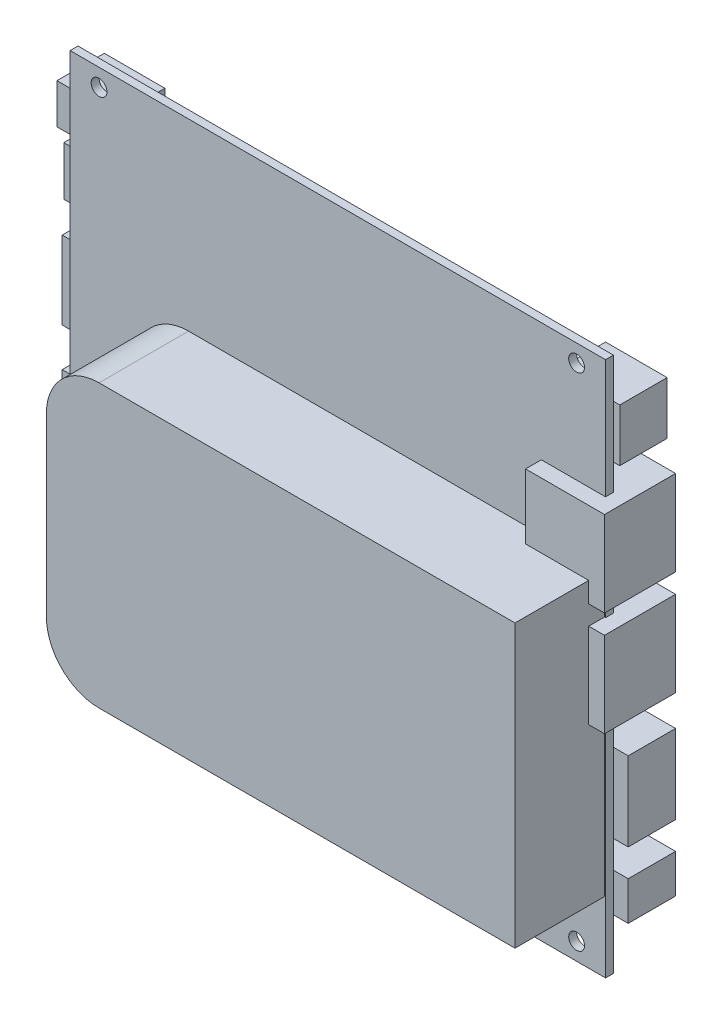
SolidWorks part; units mm, degrees
ref_plane "前视基准面" through (0, 0, 0) normal (0, 0, 1) x (1, 0, 0)
ref_plane "上视基准面" through (0, 0, 0) normal (0, 1, 0) x (1, 0, 0)
ref_plane "右视基准面" through (0, 0, 0) normal (1, 0, 0) x (0, 0, -1)
sketch "草图1" plane through (0, 0, 0) normal (0, 0, 1) x (1, 0, 0)
  line L1 (-50.85, 50.85) -> (50.85, 50.85)
  line L2 (-50.85, 50.85) -> (-50.85, -50.85)
  line L3 (-50.85, -50.85) -> (50.85, -50.85)
  line L4 (50.85, 50.85) -> (50.85, -50.85)
  line L5 (-50.85, 50.85) -> (50.85, -50.85) construction
  line L6 (-50.85, -50.85) -> (50.85, 50.85) construction
  point P0 (0, 0)
  dimension "D1" = 101.7
  dimension "D2" = 101.7
extrude "凸台-拉伸1" add sketch "草图1" along normal blind 1.5
sketch "草图2" plane through (0, 0, 0) normal (0, 0, -1) x (-1, 0, 0)
  circle A0 centre (-45.35, -47.55) radius 1.5
  circle A1 centre (45.35, -47.55) radius 1.5
  circle A2 centre (45.35, 47.55) radius 1.5
  circle A3 centre (-45.35, 47.55) radius 1.5
  dimension "D2" = 3
  dimension "D1" = 45.35
  dimension "D3" = 47.55
  dimension "D4" = 2
  dimension "D5" = 2
extrude "切除-拉伸1" cut sketch "草图2" against normal through all
sketch "草图3" plane through (0, 0, 0) normal (0, 0, -1) x (-1, 0, 0)
  line L0 (-50.85, 50.85) -> (50.85, 50.85) construction
  line L1 (43.35, 43.15) -> (54.85, 43.15)
  line L2 (43.35, 43.15) -> (43.35, 35.55)
  line L3 (43.35, 35.55) -> (54.85, 35.55)
  line L4 (54.85, 43.15) -> (54.85, 35.55)
  line L5 (44.55, 33.6) -> (53.55, 33.6)
  line L6 (44.55, 33.6) -> (44.55, 24.3)
  line L7 (44.55, 24.3) -> (53.55, 24.3)
  line L8 (53.55, 33.6) -> (53.55, 24.3)
  line L9 (37.15, 18.25) -> (53.85, 18.25)
  line L10 (37.15, 18.25) -> (37.15, 3.45)
  line L11 (37.15, 3.45) -> (53.85, 3.45)
  line L12 (53.85, 18.25) -> (53.85, 3.45)
  line L13 (37.15, -3.88) -> (53.85, -3.88)
  line L14 (37.15, -3.88) -> (37.15, -18.68)
  line L15 (37.15, -18.68) -> (53.85, -18.68)
  line L16 (53.85, -3.88) -> (53.85, -18.68)
  line L17 (48.55, -22.45) -> (54.05, -22.45)
  line L18 (48.55, -22.45) -> (48.55, -28.45)
  line L19 (48.55, -28.45) -> (54.05, -28.45)
  line L20 (54.05, -22.45) -> (54.05, -28.45)
  line L21 (41.95, -31.85) -> (55.95, -31.85)
  line L22 (41.95, -31.85) -> (41.95, -40.95)
  line L23 (41.95, -40.95) -> (55.95, -40.95)
  line L24 (55.95, -31.85) -> (55.95, -40.95)
  line L29 (50.85, 50.85) -> (50.85, -50.85) construction
  line L30 (50.85, 50.85) -> (50.85, -50.85) construction
  line L31 (-50.85, -50.85) -> (-50.85, 50.85) construction
  line L32 (-52.05, 43.26) -> (-40.35, 43.26)
  line L33 (-52.05, 43.26) -> (-52.05, 33.26)
  line L34 (-52.05, 33.26) -> (-40.35, 33.26)
  line L35 (-40.35, 43.26) -> (-40.35, 33.26)
  line L36 (-53.65, 28.29) -> (-38.65, 28.29)
  line L37 (-53.65, 28.29) -> (-53.65, 12.09)
  line L38 (-53.65, 12.09) -> (-38.65, 12.09)
  line L39 (-38.65, 28.29) -> (-38.65, 12.09)
  line L40 (-53.65, 8.42) -> (-38.65, 8.42)
  line L41 (-53.65, 8.42) -> (-53.65, -7.78)
  line L42 (-53.65, -7.78) -> (-38.65, -7.78)
  line L43 (-38.65, 8.42) -> (-38.65, -7.78)
  line L48 (-53.65, -13.65) -> (-41.15, -13.65)
  line L49 (-53.65, -13.65) -> (-53.65, -28.65)
  line L50 (-53.65, -28.65) -> (-41.15, -28.65)
  line L51 (-41.15, -13.65) -> (-41.15, -28.65)
  line L52 (-53.65, -33.87) -> (-41.95, -33.87)
  line L53 (-53.65, -33.87) -> (-53.65, -41.22)
  line L54 (-53.65, -41.22) -> (-41.95, -41.22)
  line L55 (-41.95, -33.87) -> (-41.95, -41.22)
  dimension "D1" = 7.7
  dimension "D2" = 15.3
  dimension "D3" = 17.25
  dimension "D4" = 26.55
  dimension "D5" = 32.6
  dimension "D6" = 47.4
  dimension "D7" = 54.73
  dimension "D8" = 69.53
  dimension "D9" = 73.3
  dimension "D10" = 79.3
  dimension "D11" = 82.7
  dimension "D12" = 91.8
  dimension "D13" = 11.5
  dimension "D14" = 9
  dimension "D15" = 16.7
  dimension "D16" = 16.7
  dimension "D17" = 5.5
  dimension "D18" = 14
  dimension "D19" = 4
  dimension "D20" = 2.7
  dimension "D21" = 3
  dimension "D22" = 3
  dimension "D23" = 3.2
  dimension "D24" = 5.1
  dimension "D25" = 7.59
  dimension "D26" = 17.59
  dimension "D27" = 22.56
  dimension "D28" = 38.76
  dimension "D29" = 42.43
  dimension "D30" = 58.63
  dimension "D31" = 64.5
  dimension "D32" = 79.5
  dimension "D33" = 84.72
  dimension "D34" = 92.07
  dimension "D35" = 11.7
  dimension "D36" = 15
  dimension "D37" = 15
  dimension "D38" = 12.5
  dimension "D39" = 11.7
  dimension "D40" = 1.2
  dimension "D41" = 2.8
extrude "凸台-拉伸2" add sketch "草图3" along normal blind 9
sketch "草图4" plane through (0, 0, -9) normal (0, 0, -1) x (-1, 0, 0)
  line L4 (44.55, 33.6) -> (44.55, 24.3)
  line L5 (44.55, 24.3) -> (53.55, 24.3)
  line L6 (53.55, 24.3) -> (53.55, 33.6)
  line L7 (53.55, 33.6) -> (44.55, 33.6)
  line L8 (44.55, 33.6) -> (44.55, 24.3)
  line L9 (44.55, 24.3) -> (53.55, 24.3)
  line L10 (53.55, 24.3) -> (53.55, 33.6)
  line L11 (53.55, 33.6) -> (44.55, 33.6)
  dimension "D1" = 0
extrude "切除-拉伸2" cut sketch "草图4" against normal blind 4.1
sketch "草图5" plane through (0, 0, -9) normal (0, 0, -1) x (-1, 0, 0)
  line L4 (37.15, 18.25) -> (37.15, 3.45)
  line L5 (37.15, 3.45) -> (53.85, 3.45)
  line L6 (53.85, 3.45) -> (53.85, 18.25)
  line L7 (53.85, 18.25) -> (37.15, 18.25)
  line L8 (37.15, 18.25) -> (37.15, 3.45)
  line L9 (37.15, 3.45) -> (53.85, 3.45)
  line L10 (53.85, 3.45) -> (53.85, 18.25)
  line L11 (53.85, 18.25) -> (37.15, 18.25)
  line L12 (37.15, -3.88) -> (37.15, -18.68)
  line L13 (37.15, -18.68) -> (53.85, -18.68)
  line L14 (53.85, -18.68) -> (53.85, -3.88)
  line L15 (53.85, -3.88) -> (37.15, -3.88)
  line L16 (37.15, -3.88) -> (37.15, -18.68)
  line L17 (37.15, -18.68) -> (53.85, -18.68)
  line L18 (53.85, -18.68) -> (53.85, -3.88)
  line L19 (53.85, -3.88) -> (37.15, -3.88)
  dimension "D1" = 0
  dimension "D2" = 0
extrude "切除-拉伸3" cut sketch "草图5" against normal blind 0.3
sketch "草图7" plane through (0, 0, -9) normal (0, 0, -1) x (-1, 0, 0)
  line L4 (41.95, -31.85) -> (41.95, -40.95)
  line L5 (41.95, -40.95) -> (55.95, -40.95)
  line L6 (55.95, -40.95) -> (55.95, -31.85)
  line L7 (55.95, -31.85) -> (41.95, -31.85)
  line L8 (41.95, -31.85) -> (41.95, -40.95)
  line L9 (41.95, -40.95) -> (55.95, -40.95)
  line L10 (55.95, -40.95) -> (55.95, -31.85)
  line L11 (55.95, -31.85) -> (41.95, -31.85)
  dimension "D1" = 0
extrude "切除-拉伸4" cut sketch "草图7" against normal blind 3
sketch "草图8" plane through (0, 0, -9) normal (0, 0, -1) x (-1, 0, 0)
  line L0 (-53.65, 8.42) -> (-53.65, -7.78) construction
  line L1 (-53.65, -7.78) -> (-38.65, -7.78) construction
  line L2 (-38.65, -7.78) -> (-38.65, 8.42) construction
  line L3 (-38.65, 8.42) -> (-53.65, 8.42) construction
  line L4 (-53.65, 28.29) -> (-53.65, 12.09) construction
  line L5 (-53.65, 12.09) -> (-38.65, 12.09) construction
  line L6 (-38.65, 12.09) -> (-38.65, 28.29) construction
  line L7 (-38.65, 28.29) -> (-53.65, 28.29) construction
  line L8 (-53.65, 8.42) -> (-53.65, -7.78)
  line L9 (-53.65, -7.78) -> (-38.65, -7.78)
  line L10 (-38.65, -7.78) -> (-38.65, 8.42)
  line L11 (-38.65, 8.42) -> (-53.65, 8.42)
  line L12 (-53.65, 28.29) -> (-53.65, 12.09)
  line L13 (-53.65, 12.09) -> (-38.65, 12.09)
  line L14 (-38.65, 12.09) -> (-38.65, 28.29)
  line L15 (-38.65, 28.29) -> (-53.65, 28.29)
extrude "凸台-拉伸4" add sketch "草图8" against normal blind 13.5
sketch "草图9" plane through (0, 0, 1.5) normal (0, 0, 1) x (1, 0, 0)
  line L0 (50.85, 28.29) -> (50.85, 50.85) construction
  line L1 (-38.35, 15.95) -> (50.65, 15.95)
  line L2 (-38.35, 15.95) -> (-38.35, -37.55)
  line L3 (-38.35, -37.55) -> (50.65, -37.55)
  line L4 (50.65, 15.95) -> (50.65, -37.55)
  line L5 (-50.85, -50.85) -> (50.85, -50.85) construction
  dimension "D1" = 53.5
  dimension "D2" = 89
  dimension "D3" = 0.2
  dimension "D4" = 13.3
extrude "凸台-拉伸5" add sketch "草图9" along normal blind 17
fillet "圆角1" radius 10 2 edges at (-38.35, -37.55, 10) (-38.35, 15.95, 10)
